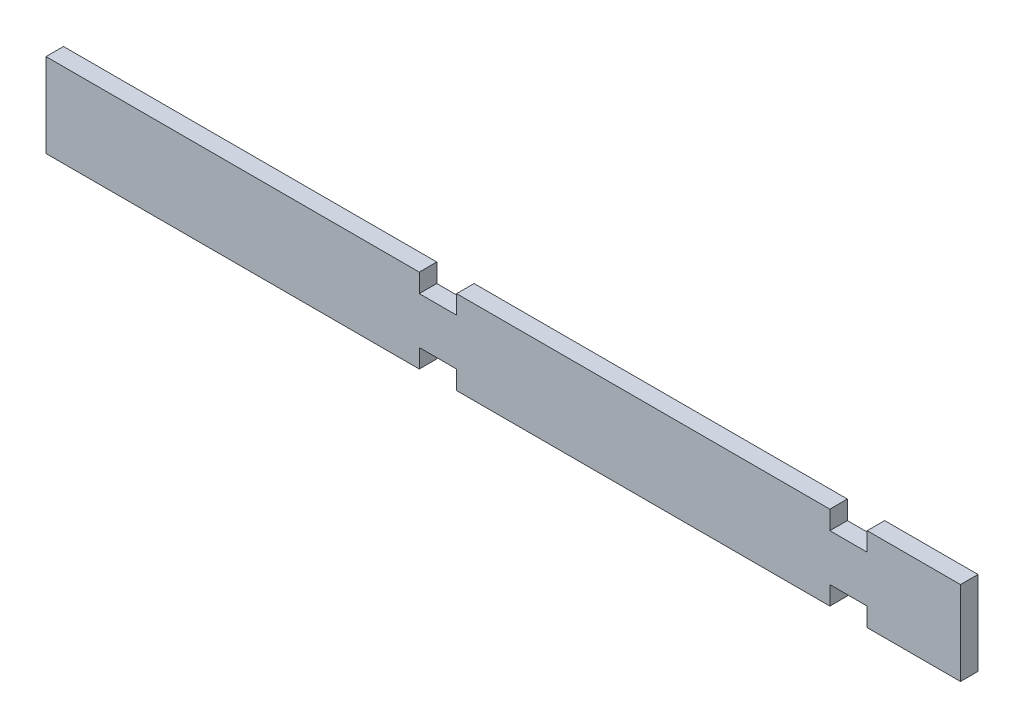
SolidWorks part; units mm, degrees
ref_plane "Front Plane" through (0, 0, 0) normal (0, 0, 1) x (1, 0, 0)
ref_plane "Top Plane" through (0, 0, 0) normal (0, 1, 0) x (1, 0, 0)
ref_plane "Right Plane" through (0, 0, 0) normal (1, 0, 0) x (0, 0, -1)
sketch "Sketch2" plane through (0, 0, 0) normal (0, 0, 1) x (1, 0, 0)
  line L0 (55, 0) -> (-55, 0) construction
  line L1 (-62.23, -5.715) -> (62.23, -5.715)
  line L2 (-62.23, -5.715) -> (-62.23, 5.715)
  line L3 (-62.23, 5.715) -> (62.23, 5.715)
  line L4 (62.23, -5.715) -> (62.23, 5.715)
  line L5 (-62.23, -5.715) -> (62.23, 5.715) construction
  line L6 (-62.23, 5.715) -> (62.23, -5.715) construction
  line L7 (-11.43, 5.715) -> (-6.35, 5.715)
  line L8 (-11.43, 5.715) -> (-11.43, 3.175)
  line L9 (-11.43, 3.175) -> (-6.35, 3.175)
  line L10 (-6.35, 5.715) -> (-6.35, 3.175)
  line L11 (44.45, 5.715) -> (49.53, 5.715)
  line L12 (44.45, 5.715) -> (44.45, 3.175)
  line L13 (44.45, 3.175) -> (49.53, 3.175)
  line L14 (49.53, 5.715) -> (49.53, 3.175)
  line L15 (49.53, -5.715) -> (49.53, -3.175)
  line L16 (44.45, -3.175) -> (49.53, -3.175)
  line L17 (44.45, -5.715) -> (44.45, -3.175)
  line L18 (-6.35, -5.715) -> (-6.35, -3.175)
  line L19 (-11.43, -3.175) -> (-6.35, -3.175)
  line L20 (-11.43, -5.715) -> (-11.43, -3.175)
  point P0 (0, 0)
  dimension "D1" = 124.46
  dimension "D2" = 11.43
  dimension "D3" = 5.08
  dimension "D4" = 5.08
  dimension "D5" = 50.8
  dimension "D6" = 12.7
  dimension "D7" = 2.54
extrude "Boss-Extrude1" add sketch "Sketch2" along normal mid plane 2.3813 contours L1 L20 L19 L18 L17 L16 L15 L4 L3 L14 L13 L12 L10 L9 L8 L2
